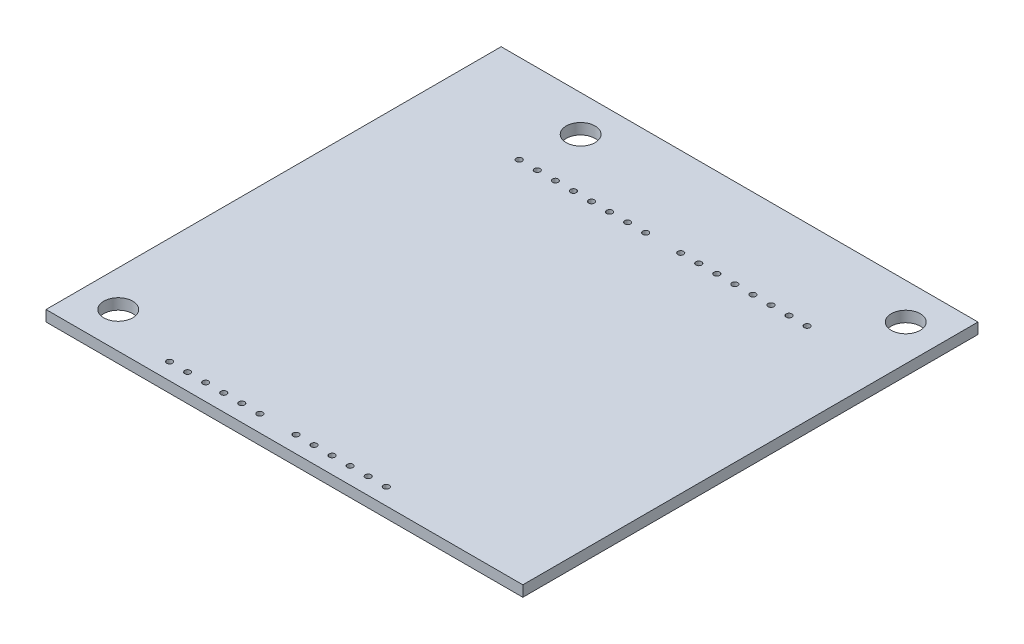
SolidWorks part; units mm, degrees
ref_plane "Front Plane" through (0, 0, 0) normal (0, 0, 1) x (1, 0, 0)
ref_plane "Top Plane" through (0, 0, 0) normal (0, 1, 0) x (1, 0, 0)
ref_plane "Right Plane" through (0, 0, 0) normal (1, 0, 0) x (0, 0, -1)
sketch "Sketch1" plane through (0, 0, 0) normal (0, 1, 0) x (1, 0, 0)
  line L0 (-28, 0) -> (28, 0) construction
  line L1 (-28, -26.5) -> (28, -26.5)
  line L2 (-28, -26.5) -> (-28, 26.5) construction
  line L3 (-28, 26.5) -> (28, 26.5) construction
  line L4 (28, -26.5) -> (28, 26.5)
  line L5 (-28, -26.5) -> (28, 26.5) construction
  line L6 (-28, 26.5) -> (28, -26.5) construction
  line L7 (-8.2, -26.5) -> (-8.2, -21.7058) construction
  line L8 (-5.7, 24.2) -> (-0.85, 24.2) construction
  line L9 (-23.2, 24.2) -> (-5.7, 24.2) construction
  line L10 (-0.85, 24.2) -> (16.65, 24.2) construction
  line L11 (-28, -26.5) -> (-38, -26.5)
  line L12 (-38, -26.5) -> (-38, 36.5)
  line L13 (-38, 36.5) -> (28, 36.5)
  line L14 (28, 36.5) -> (28, 26.5)
  line L16 (-22, 31.5) -> (23, 31.5) construction
  circle A0 centre (-23.2, 24.2) radius 0.4
  circle A1 centre (-20.7, 24.2) radius 0.4
  circle A2 centre (-18.2, 24.2) radius 0.4
  circle A3 centre (-15.7, 24.2) radius 0.4
  circle A4 centre (-13.2, 24.2) radius 0.4
  circle A5 centre (-10.7, 24.2) radius 0.4
  circle A6 centre (-8.2, 24.2) radius 0.4
  circle A7 centre (-5.7, 24.2) radius 0.4
  circle A8 centre (-10.7, -24.2) radius 0.4
  circle A9 centre (-13.2, -24.2) radius 0.4
  circle A10 centre (-15.7, -24.2) radius 0.4
  circle A11 centre (-18.2, -24.2) radius 0.4
  circle A12 centre (-20.7, -24.2) radius 0.4
  circle A13 centre (-23.2, -24.2) radius 0.4
  circle A14 centre (6.8, -24.2) radius 0.4
  circle A15 centre (4.3, -24.2) radius 0.4
  circle A16 centre (1.8, -24.2) radius 0.4
  circle A17 centre (-0.7, -24.2) radius 0.4
  circle A18 centre (-3.2, -24.2) radius 0.4
  circle A19 centre (-5.7, -24.2) radius 0.4
  circle A20 centre (-0.85, 24.2) radius 0.4
  circle A21 centre (1.65, 24.2) radius 0.4
  circle A22 centre (4.15, 24.2) radius 0.4
  circle A23 centre (6.65, 24.2) radius 0.4
  circle A24 centre (9.15, 24.2) radius 0.4
  circle A25 centre (11.65, 24.2) radius 0.4
  circle A26 centre (14.15, 24.2) radius 0.4
  circle A27 centre (16.65, 24.2) radius 0.4
  circle A28 centre (-22, 31.5) radius 2
  circle A29 centre (23, 31.5) radius 2
  circle A30 centre (-33, -21.5) radius 2
  point P0 (0, 0)
  dimension "D1" = 0.8
  dimension "D11" = 4
  dimension "D19" = 0.8
  dimension "D2" = 4.8
  dimension "D3" = 56
  dimension "D4" = 53
  dimension "D5" = 2.3
  dimension "D7" = 2.5
  dimension "D8" = 2.5
  dimension "D9" = 5
  dimension "D10" = 5
  dimension "D12" = 10
  dimension "D13" = 10
  dimension "D14" = 5
  dimension "D15" = 5
  dimension "D16" = 4.85
  dimension "D17" = 8
  dimension "D18" = 2.5
  dimension "D20" = 45
  dimension "D6" = 8
extrude "Boss-Extrude1" add sketch "Sketch1" along normal blind 1.5
